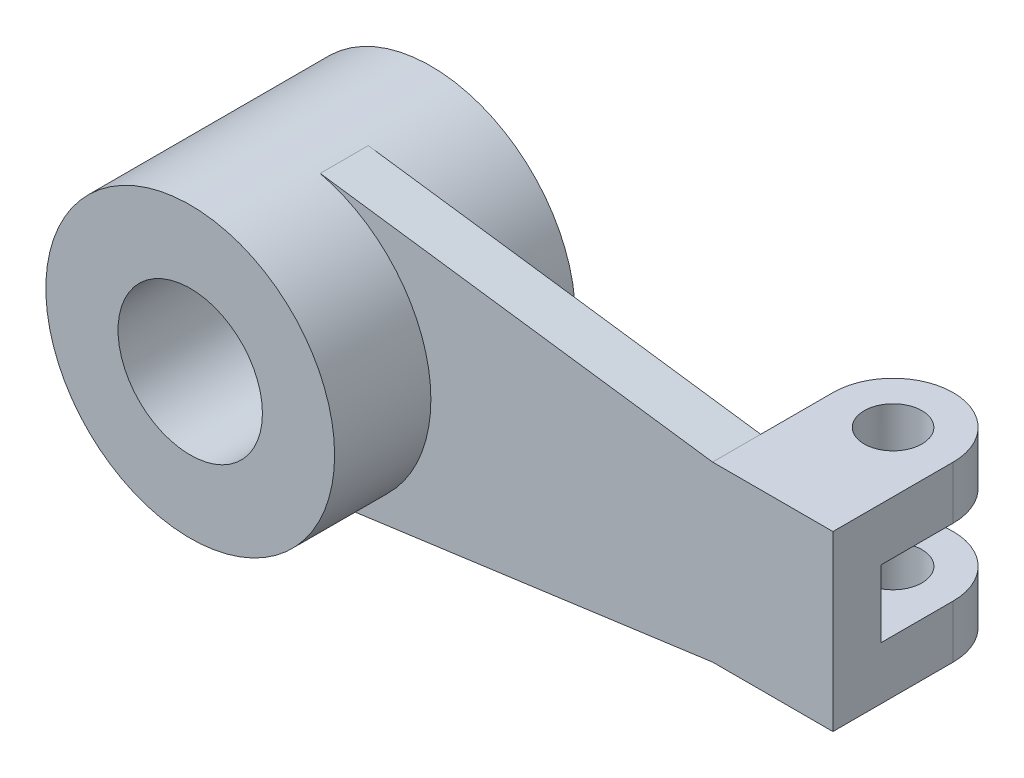
SolidWorks part; units mm, degrees
ref_plane "Front Plane" through (0, 0, 0) normal (0, 0, 1) x (1, 0, 0)
ref_plane "Top Plane" through (0, 0, 0) normal (0, 1, 0) x (1, 0, 0)
ref_plane "Right Plane" through (0, 0, 0) normal (1, 0, 0) x (0, 0, -1)
sketch "Sketch2" plane through (0, 0, 0) normal (0, 0, 1) x (1, 0, 0)
  circle A0 centre (0, 0) radius 15
  circle A1 centre (0, 0) radius 30
  dimension "D1" = 60
  dimension "D2" = 30
extrude "Boss-Extrude1" add sketch "Sketch2" along normal mid plane 50
sketch "Sketch3" plane through (0, 0, 0) normal (0, 0, 1) x (1, 0, 0)
  line L0 (0, 0) -> (113.5337, 0) construction
  line L1 (113.5337, 0) -> (113.5337, 18)
  line L2 (113.5337, 18) -> (88.5337, 18)
  line L5 (113.5337, 0) -> (113.5337, -18)
  line L6 (113.5337, -18) -> (88.5337, -18)
  line L9 (88.5337, 18) -> (6.9956, 29.173)
  line L10 (88.5337, -18) -> (7.337, -29.089)
  circle A0 centre (0, 0) radius 30 construction
  circle A2 centre (0, 0) radius 30
  arc A3 (7.337, -29.089) -> (6.9956, 29.173) centre (0, 0) ccw
  dimension "D1" = 25
  dimension "D2" = 0
extrude "Boss-Extrude2" add sketch "Sketch3" along normal mid plane 10
sketch "Sketch4" plane through (0, 18, 0) normal (0, 1, 0) x (1, 0, 0)
  line L0 (88.5337, 5) -> (113.5337, 5)
  line L1 (88.5337, 5) -> (88.5337, 20)
  line L2 (113.5337, 5) -> (113.5337, 20)
  line L3 (88.5337, 20) -> (113.5337, 20)
  arc A0 (113.5337, 20) -> (88.5337, 20) centre (101.0337, 20) ccw
  circle A1 centre (101.0337, 20) radius 6
  line M1 (113.5337, 5) -> (88.5337, 5)
  dimension "D1" = 15
extrude "Boss-Extrude3" add sketch "Sketch4" against normal blind 36 contours A1 L3 L1 L2 M1 | A1 L3 A0
sketch "Sketch5" plane through (113.5337, 0, 0) normal (1, 0, 0) x (0, 0, -1)
  line L0 (0, 0) -> (31.1789, 0)
  line L1 (5, 7) -> (40, 7)
  line L3 (40, 7) -> (40, -7)
  line L4 (5, 7) -> (5, -7)
  line L5 (-5, -18) -> (-5, 18) construction
  line L6 (40, 0) -> (5, 0)
  line L7 (5, -7) -> (40, -7)
  line M2 (20, -18) -> (20, 18)
  dimension "D1" = 10
  dimension "D2" = 7
  dimension "D3" = 35
extrude "Cut-Extrude1" cut sketch "Sketch5" against normal blind 36 contours L4 L7 L0 M2 | L1 L4 L0 M2 | L6 L3 L1 L0 M2 | L7 L3 L6 L0 M2
